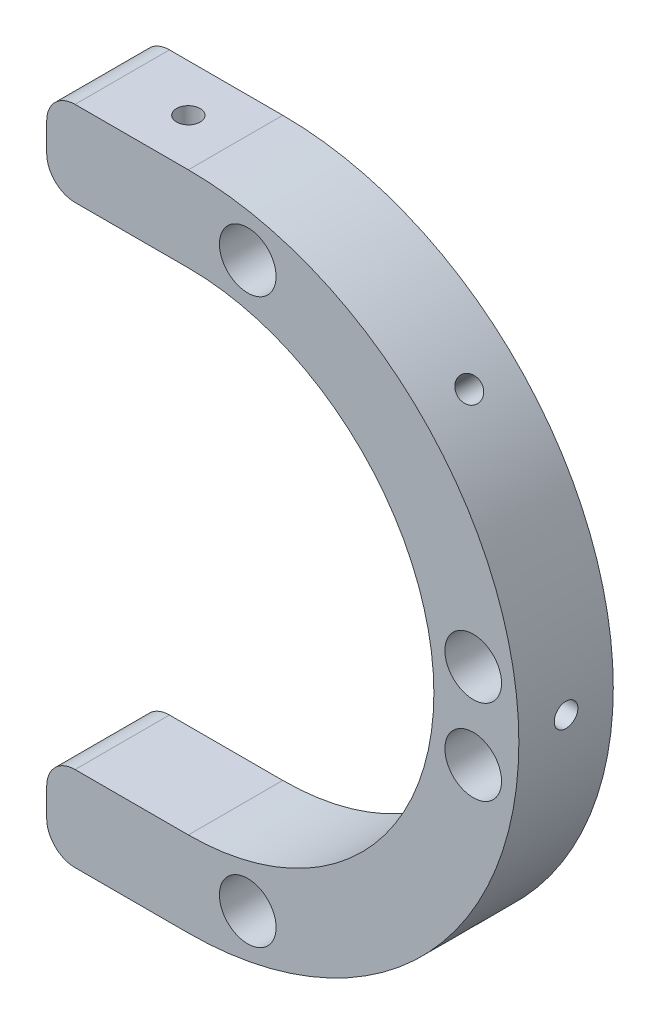
SolidWorks part; units mm, degrees
material "7050-T73510"
ref_plane "Front Plane" through (0, 0, 0) normal (0, 0, 1) x (1, 0, 0)
ref_plane "Top Plane" through (0, 0, 0) normal (0, 1, 0) x (1, 0, 0)
ref_plane "Right Plane" through (0, 0, 0) normal (1, 0, 0) x (0, 0, -1)
sketch "Sketch1" plane through (0, 0, 0) normal (0, 0, 1) x (1, 0, 0)
  line L0 (0, 35) -> (-15, 35)
  line L1 (-15, 35) -> (-15, -35)
  line L2 (-15, -35) -> (0, -35)
  line L3 (6.2896, 25.2278) -> (-15, 20)
  line L4 (6.2896, -25.2278) -> (-15, -20)
  line L5 (35, 0) -> (-35, 0) construction
  line L6 (30.1662, 4.5) -> (30.1662, -4.5) construction
  line L7 (0, 26) -> (-15, 26)
  line L8 (0, -26) -> (-15, -26)
  line L9 (-15, 20) -> (-15, 26)
  circle A0 centre (0, 0) radius 35
  circle A1 centre (0, 0) radius 26
  circle A2 centre (30.1662, 4.5) radius 3
  circle A3 centre (30.1662, -4.5) radius 3
  circle A4 centre (6.2896, 29.8444) radius 3
  circle A5 centre (6.2896, -29.8444) radius 3
  circle A6 centre (0, 0) radius 30.5 construction
  dimension "D1" = 70
  dimension "D2" = 9
  dimension "D3" = 6
  dimension "D4" = 4.5
  dimension "D5" = 6
  dimension "D6" = 6
  dimension "D7" = 6
  dimension "D8" = 9
  dimension "D9" = 34.82
  dimension "D10" = 50
  dimension "D11" = 15
extrude "Boss-Extrude1" add sketch "Sketch1" along normal blind 10 contours A1 L8 L1 A0 L7 A5 A4 A3 A2 | A0 L0 L1 | A0 L1 L2
fillet "Fillet1" radius 3 4 edges at (-15, -35, 5) (-15, 35, 5) (-15, 26, 5) (-15, -26, 5)
sketch "Sketch12" plane through (0, 0, 0) normal (0, 1, 0) x (1, 0, 0)
  line L0 (35, -10) -> (35, 0)
  line L1 (35, 0) -> (0, 0) construction
  line L2 (35, -10) -> (35, 0) construction
sketch "Sketch13" plane through (0, 0, 0) normal (0, 0, 1) x (1, 0, 0)
  line L0 (35, 0) -> (35, 7.0857)
  arc A0 (0, -35) -> (0, 35) centre (0, 0) ccw construction
ref_plane "Plane1" through (35, 0, 0) normal (1, 0, 0) x (0, 0, -1)
hole_wizard "M3 Tapped Hole3" positions "Sketch15" profile "Sketch14" tap size "M3" standard "ISO"
sketch "Sketch15" plane through (35, 0, 0) normal (1, 0, 0) x (0, 0, -1)
  line L0 (-10, 35) -> (-10, -35) construction
  point P0 (-5, 0)
  point P5 (-10, 0)
  dimension "D1" = 5
  dimension "D2" = 0
sketch "Sketch14" plane through (35, 0, 5) normal (0, 1, 0) x (0, 0, -1)
  line L0 (0, 0) -> (0, 8.2511)
  line L1 (0, 8.2511) -> (1.25, 7.5)
  line L2 (1.25, 7.5) -> (1.25, 0)
  line L5 (1.25, 0) -> (0, 0)
  line L10 (0, 8.2511) -> (-1.25, 7.5) construction
  line L11 (0, -6.35) -> (0, 107.95) construction
  dimension "Tap Drill Dia." = 2.5
  dimension "Tap Drill Depth" = 7.5
  dimension "Drill Angle" = 118
cosmetic thread "Hole Thread3" parameters "D1"=7.5, "D2"=3
pattern_circular "CirPattern1" count 2 every 45 about axis through (0, 0, 0) along (0, 0, 1) of "M3 Tapped Hole3"
pattern_circular "CirPattern2" count 2 every 45 about axis through (0, 0, 10) along (0, 0, 1) of "M3 Tapped Hole3"
hole_wizard "M3 Tapped Hole4" positions "3DSketch1" profile "Sketch16" tap size "M3" standard "ISO"
sketch3d "3DSketch1"
  line L0 (-12, -35, 10) -> (0, -35, 10) construction
  line L1 (0, 35, 10) -> (-12, 35, 10) construction
  point P0 (-5, -35, 5)
  point P2 (-5, 35, 5)
  dimension "D1" = 10
  dimension "D2" = 10
  dimension "D3" = 5
  dimension "D4" = 5
sketch "Sketch16" plane through (-5, -35, 5) normal (1, 0, 0) x (0, 0, -1)
  line L0 (0, 0) -> (0, 8.2511)
  line L1 (0, 8.2511) -> (1.25, 7.5)
  line L2 (1.25, 7.5) -> (1.25, 0)
  line L5 (1.25, 0) -> (0, 0)
  line L10 (0, 8.2511) -> (-1.25, 7.5) construction
  line L11 (0, -6.35) -> (0, 107.95) construction
  dimension "Tap Drill Dia." = 2.5
  dimension "Tap Drill Depth" = 7.5
  dimension "Drill Angle" = 118
cosmetic thread "Hole Thread4" parameters "D1"=6, "D2"=3
cosmetic thread "Hole Thread5" parameters "D1"=6, "D2"=3
